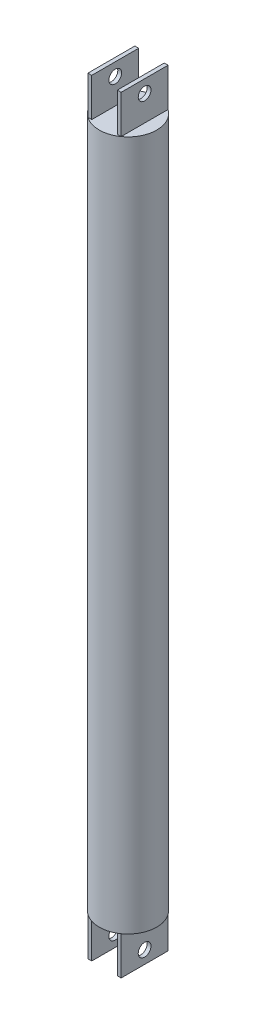
SolidWorks part; units mm, degrees
material "Titanium"
ref_plane "Front Plane" through (0, 0, 0) normal (0, 0, 1) x (1, 0, 0)
ref_plane "Top Plane" through (0, 0, 0) normal (0, 1, 0) x (1, 0, 0)
ref_plane "Right Plane" through (0, 0, 0) normal (1, 0, 0) x (0, 0, -1)
sketch "Sketch1" plane through (0, 0, 0) normal (0, 1, 0) x (1, 0, 0)
  circle A0 centre (0, 0) radius 22.5
  circle A1 centre (0, 0) radius 20.5
  dimension "D1" = 45
  dimension "D2" = 2
extrude "Extrude1" add sketch "Sketch1" along normal blind 500
sketch "Sketch2" plane through (0, 500, 0) normal (0, 1, 0) x (-1, 0, 0)
  circle A0 centre (0, 0) radius 22.5
  circle A1 centre (0, 0) radius 22.5 construction
extrude "Extrude2" add sketch "Sketch2" along normal blind 20
sketch "Sketch3" plane through (0, 0, 0) normal (0, -1, 0) x (1, 0, 0)
  circle A0 centre (0, 0) radius 22.5
  circle A1 centre (0, 0) radius 22.5 construction
extrude "Extrude3" add sketch "Sketch3" along normal blind 20
sketch "Sketch5" plane through (0, -20, 0) normal (0, -1, 0) x (1, 0, 0)
  line L1 (-13, 18.3644) -> (-10, 18.3644)
  line L2 (-13, 18.3644) -> (-13, -18.3644)
  line L3 (-13, -18.3644) -> (-10, -18.3644)
  line L4 (-10, 18.3644) -> (-10, -18.3644)
  line L5 (13, 18.3644) -> (10, 18.3644)
  line L6 (13, 18.3644) -> (13, -18.3644)
  line L7 (13, -18.3644) -> (10, -18.3644)
  line L8 (10, 18.3644) -> (10, -18.3644)
  circle A0 centre (0, 0) radius 22.5 construction
  dimension "D1" = 3
  dimension "D2" = 3
  dimension "D3" = 10
extrude "Extrude4" add sketch "Sketch5" along normal blind 30
sketch "Sketch7" plane through (0, 520, 0) normal (0, 1, 0) x (-1, 0, 0)
  line L1 (-13, 18.3644) -> (-10, 18.3644)
  line L2 (-13, 18.3644) -> (-13, -18.3644)
  line L3 (-13, -18.3644) -> (-10, -18.3644)
  line L4 (-10, 18.3644) -> (-10, -18.3644)
  line L5 (10, 18.3644) -> (13, 18.3644)
  line L6 (10, 18.3644) -> (10, -18.3644)
  line L7 (10, -18.3644) -> (13, -18.3644)
  line L8 (13, 18.3644) -> (13, -18.3644)
extrude "Extrude6" add sketch "Sketch7" along normal blind 30
sketch "Sketch8" plane through (-13, 0, 0) normal (-1, 0, 0) x (0, 0, 1)
  line L0 (-18.3644, 550) -> (18.3644, 550) construction
  circle A0 centre (0, 540) radius 5
  dimension "D1" = 10
  dimension "D2" = 10
extrude "Cut-Extrude1" cut sketch "Sketch8" against normal through all and the other way through all
sketch "Sketch9" plane through (-13, 0, 0) normal (-1, 0, 0) x (0, 0, 1)
  line L0 (18.3644, -50) -> (-18.3644, -50) construction
  circle A0 centre (0, -40) radius 5
  point P2 (0, -50)
  dimension "D1" = 10
  dimension "D2" = 10
extrude "Cut-Extrude2" cut sketch "Sketch9" against normal through all and the other way through all
